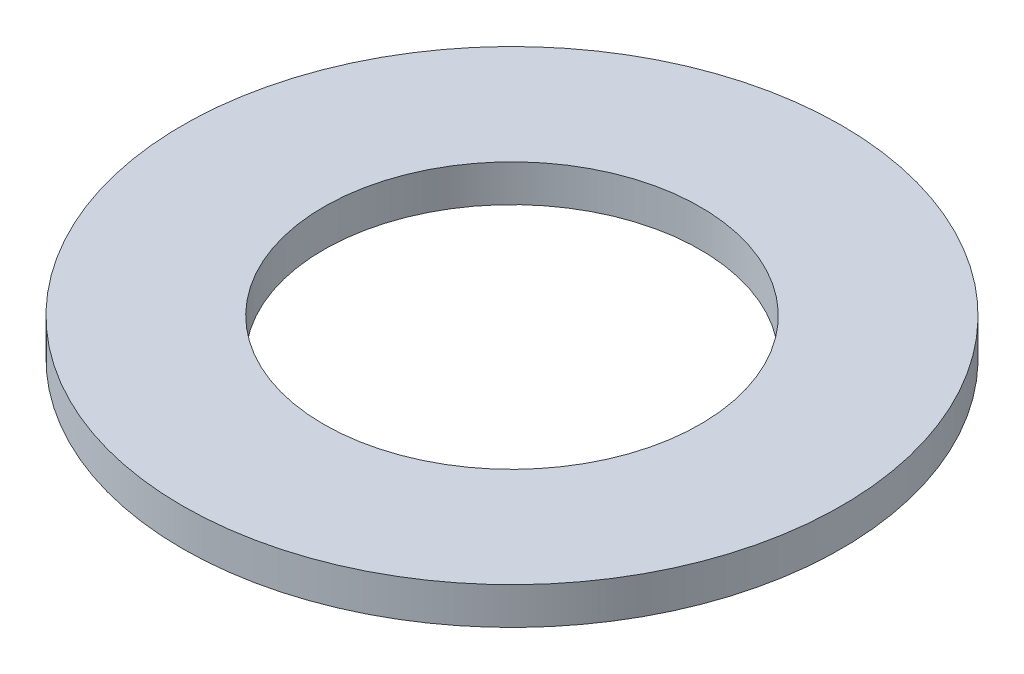
SolidWorks part; units mm, degrees
ref_plane "Front Plane" through (0, 0, 0) normal (0, 0, 1) x (1, 0, 0)
ref_plane "Top Plane" through (0, 0, 0) normal (0, 1, 0) x (1, 0, 0)
ref_plane "Right Plane" through (0, 0, 0) normal (1, 0, 0) x (0, 0, -1)
sketch "Sketch2" plane through (0, 0, 0) normal (0, 1, 0) x (1, 0, 0)
  circle A0 centre (0, 0) radius 88.9
  circle A1 centre (0, 0) radius 50.8
  dimension "D1" = 177.8
  dimension "D2" = 101.6
extrude "Boss-Extrude1" add sketch "Sketch2" along normal blind 10 contours A0
sketch "Sketch4" plane through (0, 0, 0) normal (0, 1, 0) x (1, 0, 0)
  circle A0 centre (0, 0) radius 50.8
  dimension "D1" = 101.6
extrude "Cut-Extrude1" cut sketch "Sketch4" along normal blind 15
